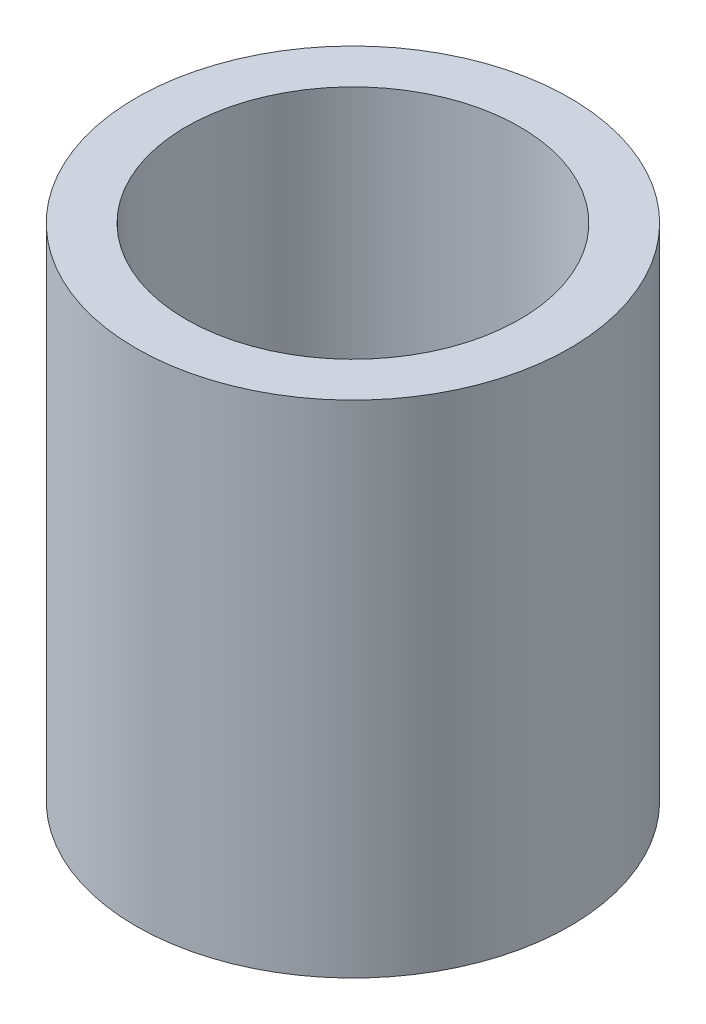
SolidWorks part; units mm, degrees
ref_plane "Front Plane" through (0, 0, 0) normal (0, 0, 1) x (1, 0, 0)
ref_plane "Top Plane" through (0, 0, 0) normal (0, 1, 0) x (1, 0, 0)
ref_plane "Right Plane" through (0, 0, 0) normal (1, 0, 0) x (0, 0, -1)
sketch "Sketch1" plane through (0, 0, 0) normal (0, 1, 0) x (1, 0, 0)
  circle A0 centre (0, 0) radius 2
  circle A2 centre (0, 0) radius 2.6
  dimension "D1" = 4
  dimension "D2" = 5.2
extrude "Boss-Extrude1" add sketch "Sketch1" along normal blind 6
